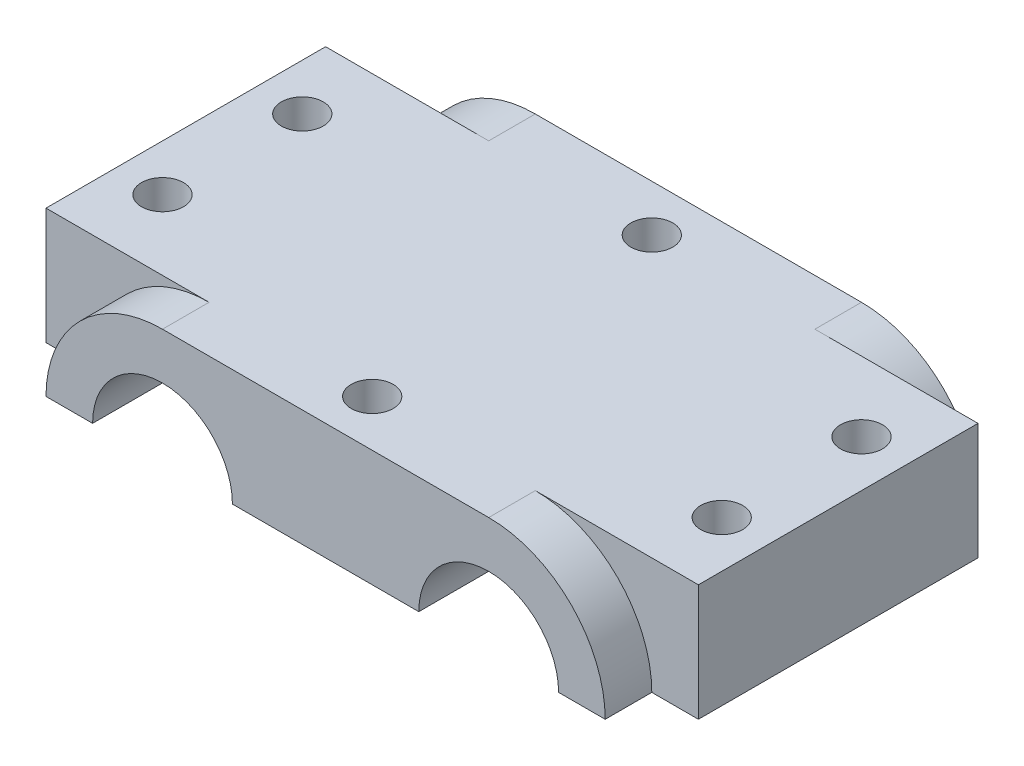
SolidWorks part; units mm, degrees
ref_plane "Front Plane" through (0, 0, 0) normal (0, 0, 1) x (1, 0, 0)
ref_plane "Top Plane" through (0, 0, 0) normal (0, 1, 0) x (1, 0, 0)
ref_plane "Right Plane" through (0, 0, 0) normal (1, 0, 0) x (0, 0, -1)
sketch "Sketch1" plane through (0, 0, 0) normal (0, 0, 1) x (1, 0, 0)
  line L0 (0, 51.865) -> (0, -51.865) construction
  line L1 (-85.1953, 0) -> (50.1953, 0) construction
  line L2 (-17.5, 51.865) -> (-17.5, -51.865) construction
  line L3 (-17.5, 12.5) -> (17.5, 12.5)
  line L4 (-10, 0) -> (10, 0)
  line L5 (-30, 0) -> (-25, 0)
  line L6 (30, 0) -> (25, 0)
  arc A0 (-25, 0) -> (-10, 0) centre (-17.5, 0) cw
  arc A1 (-30, 0) -> (-17.5, 12.5) centre (-17.5, 0) cw
  arc A2 (30, 0) -> (17.5, 12.5) centre (17.5, 0) ccw
  arc A3 (25, 0) -> (10, 0) centre (17.5, 0) ccw
  point P13 (-17.5, 0)
  point P15 (0, 12.5)
  point P21 (0, 0)
  dimension "D1" = 7.5
  dimension "D3" = 12.5
  dimension "D2" = 17.5
extrude "Boss-Extrude1" add sketch "Sketch1" along normal blind 5
sketch "Sketch2" plane through (0, 0, 0) normal (0, 0, -1) x (-1, 0, 0)
  line L0 (-17.5, 12.5) -> (17.5, 12.5) construction
  line L1 (35, 0) -> (-35, 0)
  line L2 (35, 0) -> (35, 12.5)
  line L3 (35, 12.5) -> (-35, 12.5)
  line L4 (-35, 0) -> (-35, 12.5)
  line L5 (10, 0) -> (-10, 0) construction
  line L6 (0, 22.0461) -> (0, -13.9357) construction
  dimension "D1" = 70
extrude "Boss-Extrude2" add sketch "Sketch2" along normal blind 15
sketch "Sketch3" plane through (0, 12.5, 0) normal (0, 1, 0) x (1, 0, 0)
  line L0 (17.5, 0) -> (35, 0) construction
  line L3 (35, 15) -> (35, 0) construction
  line L4 (0, 28.4778) -> (0, -14.1501) construction
  line L5 (17.5, -5) -> (-17.5, -5) construction
  circle A0 centre (0, 0) radius 2.25
  circle A2 centre (30, 7.5) radius 2.25
  circle A3 centre (-30, 7.5) radius 2.25
  dimension "D3" = 4.5
  dimension "D1" = 7.5
  dimension "D2" = 5
  dimension "D4" = 5
extrude "Cut-Extrude1" cut sketch "Sketch3" against normal blind 15
sketch "Sketch5" plane through (0, 0, 0) normal (0, 0, 1) x (1, 0, 0)
  line L1 (-25, 0) -> (-10, 0)
  line L2 (-25, 0) -> (-10, 0)
  arc A1 (-10, 0) -> (-25, 0) centre (-17.5, 0) ccw
  arc A2 (-10, 0) -> (-25, 0) centre (-17.5, 0) ccw
  dimension "D1" = 0
extrude "Cut-Extrude2" cut sketch "Sketch5" against normal blind 15
sketch "Sketch6" plane through (0, 0, 0) normal (0, 0, 1) x (1, 0, 0)
  line L1 (10, 0) -> (25, 0)
  line L2 (10, 0) -> (25, 0)
  arc A1 (25, 0) -> (10, 0) centre (17.5, 0) ccw
  arc A2 (25, 0) -> (10, 0) centre (17.5, 0) ccw
  dimension "D1" = 0
extrude "Cut-Extrude3" cut sketch "Sketch6" against normal blind 15
mirror "Mirror1" about plane through (0, 0, -15) normal (0, 0, -1) of bodies 105
